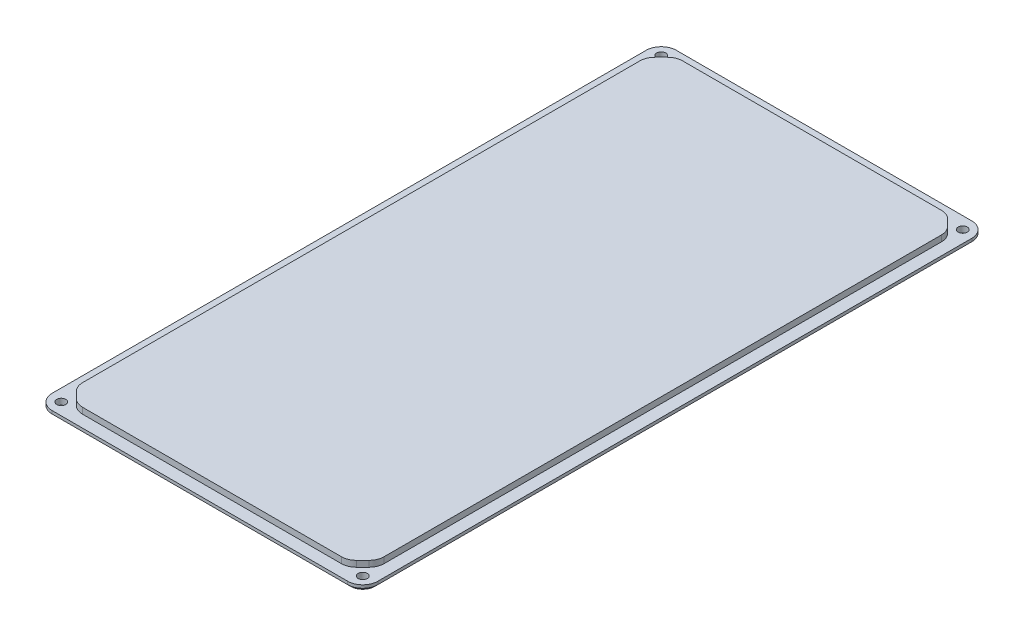
SolidWorks part; units mm, degrees
material "2014 Alloy"
ref_plane "Front Plane" through (0, 0, 0) normal (0, 0, 1) x (1, 0, 0)
ref_plane "Top Plane" through (0, 0, 0) normal (0, 1, 0) x (1, 0, 0)
ref_plane "Right Plane" through (0, 0, 0) normal (1, 0, 0) x (0, 0, -1)
sketch "Sketch1" plane through (0, 0, 0) normal (0, 1, 0) x (1, 0, 0)
  line L1 (-54, 103.5) -> (54, 103.5)
  line L2 (-54, 103.5) -> (-54, -103.5)
  line L3 (-54, -103.5) -> (54, -103.5)
  line L4 (54, 103.5) -> (54, -103.5)
  line L5 (-54, 103.5) -> (54, -103.5) construction
  line L6 (-54, -103.5) -> (54, 103.5) construction
  point P0 (0, 0)
  dimension "D1" = 108
  dimension "D2" = 207
extrude "Boss-Extrude1" add sketch "Sketch1" along normal blind 2
sketch "Sketch2" plane through (0, 2, 0) normal (0, 1, 0) x (1, 0, 0)
  line L1 (-50, 99.5) -> (50, 99.5)
  line L2 (-50, 99.5) -> (-50, -99.5)
  line L3 (-50, -99.5) -> (50, -99.5)
  line L4 (50, 99.5) -> (50, -99.5)
  line L5 (-50, 99.5) -> (50, -99.5) construction
  line L6 (-50, -99.5) -> (50, 99.5) construction
  point P0 (0, 0)
  dimension "D1" = 199
  dimension "D2" = 100
extrude "Boss-Extrude2" add sketch "Sketch2" along normal blind 2
chamfer "Chamfer1" distance 5 angle 45 4 edges at (-50, 3, -99.5) (50, 3, -99.5) (-50, 3, 99.5) (50, 3, 99.5)
fillet "Fillet1" radius 5 12 edges at (-54, 1, 103.5) (-50, 3, 94.5) (-45, 3, 99.5) (54, 1, 103.5) (50, 3, 94.5) (45, 3, 99.5) (54, 1, -103.5) (45, 3, -99.5) (50, 3, -94.5) (-45, 3, -99.5) (-50, 3, -94.5) (-54, 1, -103.5)
hole_wizard "Ø3.0mm Dowel Hole1" positions "Sketch4" profile "Sketch3" hole size "Ø3.0" standard "ISO"
sketch "Sketch4" plane through (0, 0, 0) normal (0, -1, 0) x (-1, 0, 0)
  line L0 (-54, -98.5) -> (-54, 98.5) construction
  line L1 (-49, 103.5) -> (49, 103.5) construction
  line L2 (54, 98.5) -> (54, -98.5) construction
  line L3 (49, -103.5) -> (-49, -103.5) construction
  point P0 (-50, 99.5)
  point P2 (50, 99.5)
  point P4 (50, -99.5)
  point P6 (-50, -99.5)
  dimension "D1" = 4
  dimension "D2" = 4
  dimension "D3" = 4
  dimension "D4" = 4
sketch "Sketch3" plane through (50, 0, -99.5) normal (1, 0, 0) x (0, 0, -1)
  line L0 (0, 0) -> (0, 18.1913)
  line L1 (0, 18.1913) -> (1.5, 17.29)
  line L2 (1.5, 17.29) -> (1.5, 0)
  line L5 (1.5, 0) -> (0, 0)
  line L10 (0, 18.1913) -> (-1.5, 17.29) construction
  line L11 (0, -6.35) -> (0, 107.95) construction
  dimension "Hole Dia." = 3
  dimension "Hole Depth" = 17.29
  dimension "Drill Angle" = 118
chamfer "Chamfer2" distance 1 angle 45 8 edges at (0, 0, 103.5) (52.5355, 0, 102.0355) (-52.5355, 0, 102.0355) (54, 0, 0) (-54, 0, 0) (52.5355, 0, -102.0355) (-52.5355, 0, -102.0355) (0, 0, -103.5)
